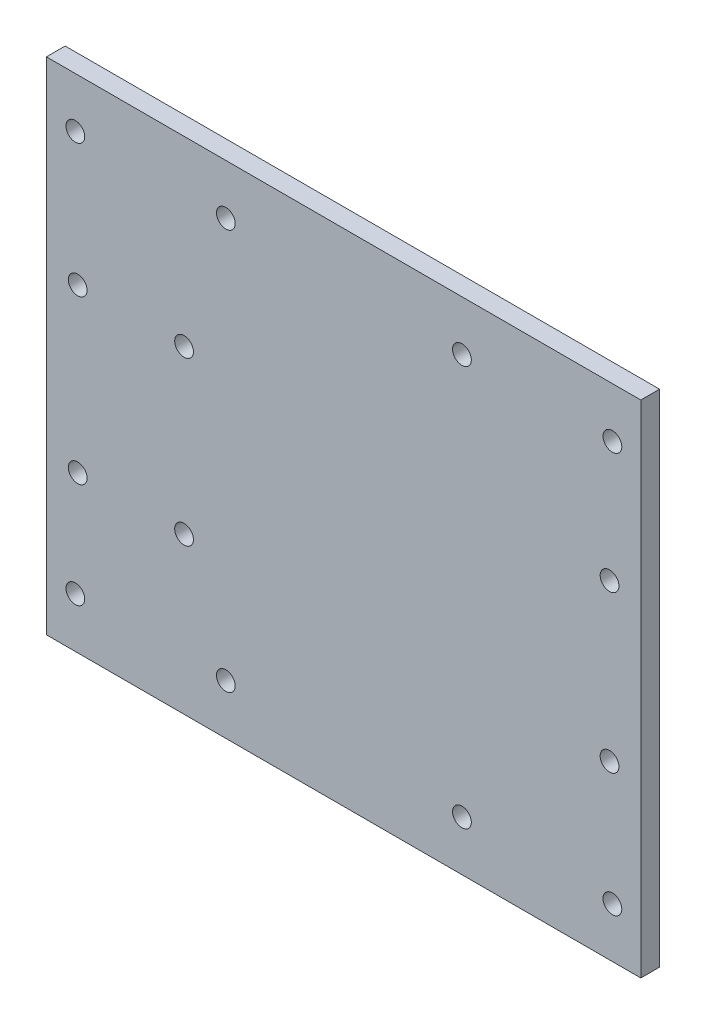
SolidWorks part; units mm, degrees
ref_plane "Front Plane" through (0, 0, 0) normal (0, 0, 1) x (1, 0, 0)
ref_plane "Top Plane" through (0, 0, 0) normal (0, 1, 0) x (1, 0, 0)
ref_plane "Right Plane" through (0, 0, 0) normal (1, 0, 0) x (0, 0, -1)
sketch "Sketch1" plane through (0, 0, 0) normal (0, 0, 1) x (1, 0, 0)
  line L1 (-47.5, -40) -> (47.5, -40)
  line L2 (-47.5, -40) -> (-47.5, 40)
  line L3 (-47.5, 40) -> (47.5, 40)
  line L4 (47.5, -40) -> (47.5, 40)
  line L5 (-47.5, -40) -> (47.5, 40) construction
  line L6 (-47.5, 40) -> (47.5, -40) construction
  point P0 (0, 0)
extrude "Boss-Extrude1" add sketch "Sketch1" along normal blind 3
sketch "Sketch2" plane through (0, 0, 3) normal (0, 0, 1) x (1, 0, 0)
  line L0 (-47.5, -40) -> (47.5, -40) construction
  line L1 (47.5, 40) -> (-47.5, 40) construction
  line L2 (-47.5, 40) -> (-47.5, -40) construction
  line L3 (47.5, -40) -> (47.5, 40) construction
  line L5 (47.5, -40) -> (47.5, 40) construction
  circle A0 centre (-42.8757, -32) radius 1.5
  circle A1 centre (-18.8257, -32) radius 1.5
  circle A2 centre (-42.8757, 32) radius 1.5
  circle A3 centre (-18.8257, 32) radius 1.5
  circle A4 centre (-42.5, 10.9277) radius 1.5
  circle A5 centre (-25.5, 10.9277) radius 1.5
  circle A6 centre (-42.5, -15.0723) radius 1.5
  circle A7 centre (-25.5, -15.0723) radius 1.5
  circle A8 centre (42.5, -12.5) radius 1.5
  circle A9 centre (42.5, 12.5) radius 1.5
  circle A10 centre (18.9097, 32) radius 1.5
  circle A11 centre (42.9597, 32) radius 1.5
  circle A12 centre (18.9097, -32) radius 1.5
  circle A13 centre (42.9597, -32) radius 1.5
  point P36 (42.9597, 30.5)
  point P37 (42.9597, 33.5)
  point P40 (0, 0)
  point P41 (0, 0)
  point P42 (42.9597, -30.5)
  dimension "D1" = 24.05
  dimension "D4" = 26
  dimension "D6" = 17
  dimension "D8" = 25
  dimension "D11" = 5
  dimension "D12" = 64
  dimension "D14" = 3
  dimension "D17" = 3
  dimension "D21" = 3
  dimension "D2" = 8
  dimension "D3" = 8
  dimension "D5" = 8
  dimension "D7" = 17
  dimension "D9" = 52.5
  dimension "D10" = 5
  dimension "D13" = 24.05
  dimension "D15" = 8
  dimension "D16" = 5
  dimension "D18" = 16.9319
  dimension "D19" = 37.7354
  dimension "D20" = 21.0757
  dimension "D22" = 24.05
  dimension "D23" = 37.7354
  dimension "D24" = 64
  dimension "D25" = 85.8354
  dimension "D26" = 85.8354
  dimension "D27" = 18
extrude "Cut-Extrude1" cut sketch "Sketch2" against normal blind 3
